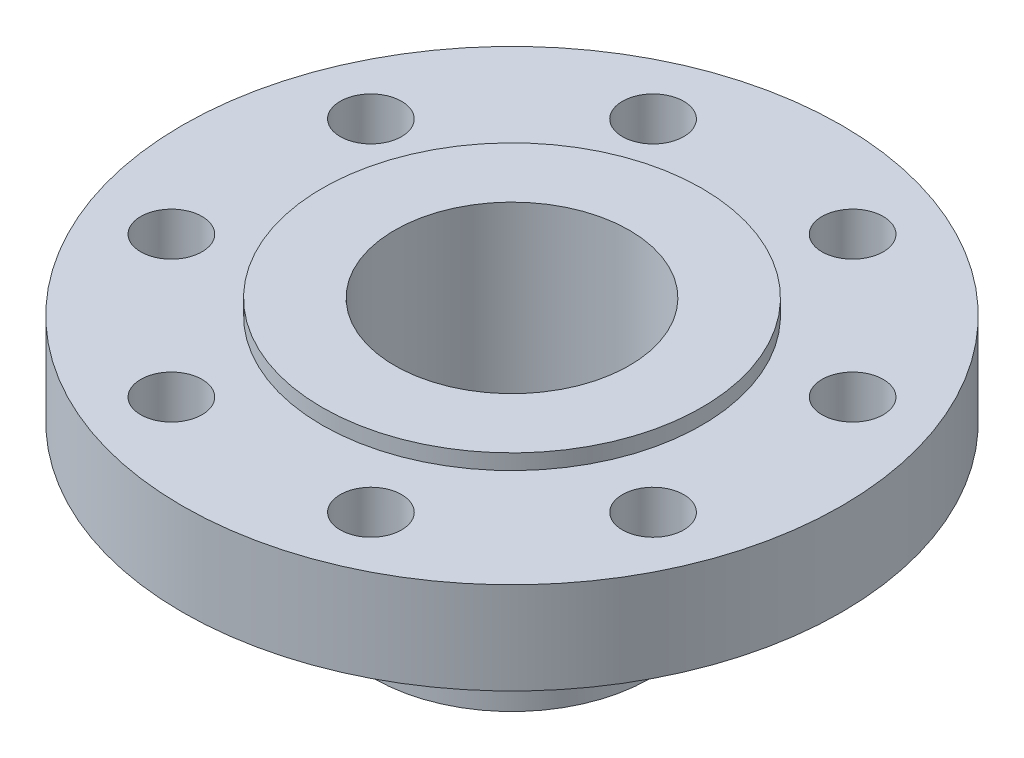
SolidWorks part; units mm, degrees
ref_plane "Plano frontal" through (0, 0, 0) normal (0, 0, 1) x (1, 0, 0)
ref_plane "Plano superior" through (0, 0, 0) normal (0, 1, 0) x (1, 0, 0)
ref_plane "Plano direito" through (0, 0, 0) normal (1, 0, 0) x (0, 0, -1)
sketch "Esboço1" plane through (0, 0, 0) normal (0, 0, 1) x (1, 0, 0)
  line L0 (0, 0) -> (0, 107.95) construction
  line L1 (48.59, 0) -> (48.59, 107.95)
  line L2 (48.59, 107.95) -> (78.615, 107.95)
  line L3 (78.615, 107.95) -> (78.615, 101.6)
  line L4 (78.615, 101.6) -> (136.525, 101.6)
  line L5 (136.525, 101.6) -> (136.525, 63.5)
  line L6 (136.525, 63.5) -> (76.2, 63.5)
  line L7 (76.2, 63.5) -> (57.15, 12.29)
  line L8 (57.15, 12.29) -> (57.15, 0)
  line L9 (57.15, 0) -> (48.59, 0)
  dimension "D1" = 107.95
  dimension "D2" = 97.18
  dimension "D3" = 157.23
  dimension "D4" = 273.05
  dimension "D5" = 114.3
  dimension "D6" = 12.29
  dimension "D7" = 6.35
  dimension "D8" = 38.1
  dimension "D9" = 152.4
revolve "Revolução1" add sketch "Esboço1" angle 360 about L0
sketch "Esboço2" plane through (0, 101.6, 0) normal (0, 1, 0) x (1, 0, 0)
  line L0 (0, 0) -> (0, 136.525) construction
  line L1 (0, 0) -> (41.3107, 99.7328) construction
  circle A0 centre (0, 0) radius 136.525 construction
  circle A1 centre (41.3107, 99.7328) radius 12.7
  dimension "D3" = 25.4
  dimension "D1" = 22.5
  dimension "D2" = 107.95
extrude "Corte-extrusão1" cut sketch "Esboço2" against normal through all contours A1
pattern_circular "PadrãoCircular1" count 8 over 360 about axis through (0, 0, 0) along (0, 1, 0) of "Corte-extrusão1"
